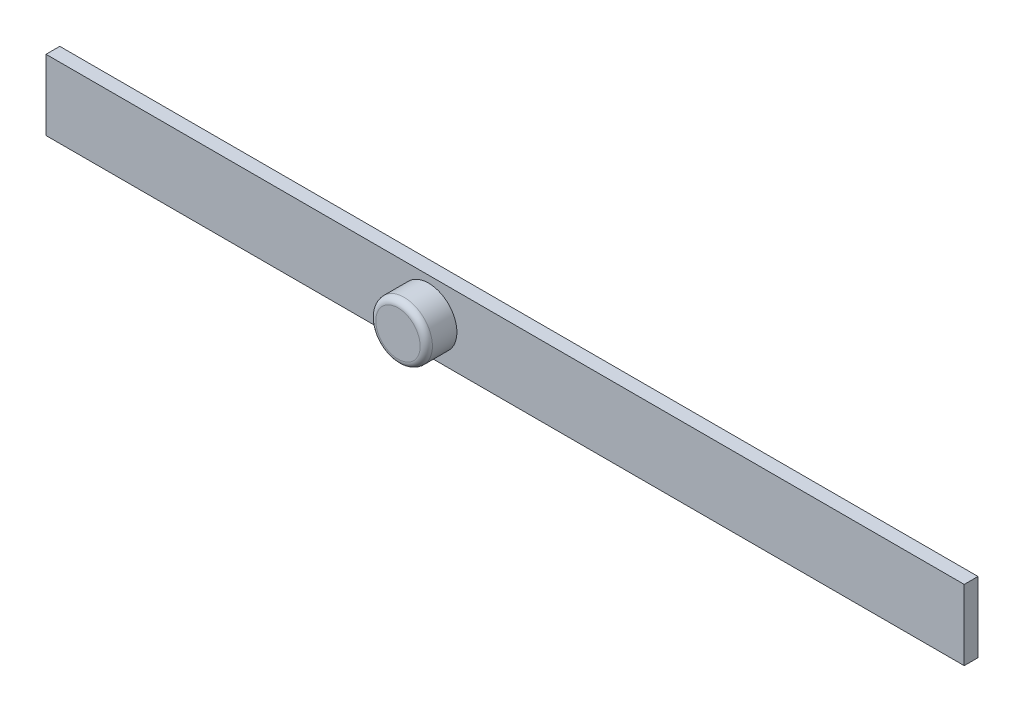
SolidWorks part; units mm, degrees
ref_plane "Přední rovina" through (0, 0, 0) normal (0, 0, 1) x (1, 0, 0)
ref_plane "Horní rovina" through (0, 0, 0) normal (0, 1, 0) x (1, 0, 0)
ref_plane "Pravá rovina" through (0, 0, 0) normal (1, 0, 0) x (0, 0, -1)
sketch "Skica1" plane through (0, 0, 0) normal (0, 0, 1) x (1, 0, 0)
  line L1 (-30, 2.3) -> (30, 2.3)
  line L2 (-30, 2.3) -> (-30, -2.3)
  line L3 (-30, -2.3) -> (30, -2.3)
  line L4 (30, 2.3) -> (30, -2.3)
  line L5 (-30, 2.3) -> (30, -2.3) construction
  line L6 (-30, -2.3) -> (30, 2.3) construction
  point P0 (0, 0)
  dimension "D1" = 4.6
  dimension "D2" = 60
extrude "Přidat vysunutím1" add sketch "Skica1" along normal blind 0.9
sketch "Skica2" plane through (0, 0, 0.9) normal (0, 0, 1) x (1, 0, 0)
  line L0 (-30, 2.3) -> (-30, -2.3) construction
  circle A0 centre (-5, 0) radius 1.85
  dimension "D1" = 3.7
  dimension "D3" = 25
extrude "Přidat vysunutím2" add sketch "Skica2" along normal blind 2
fillet "Zaoblit1" radius 0.4 1 edges at (-3.15, 0, 2.9)
